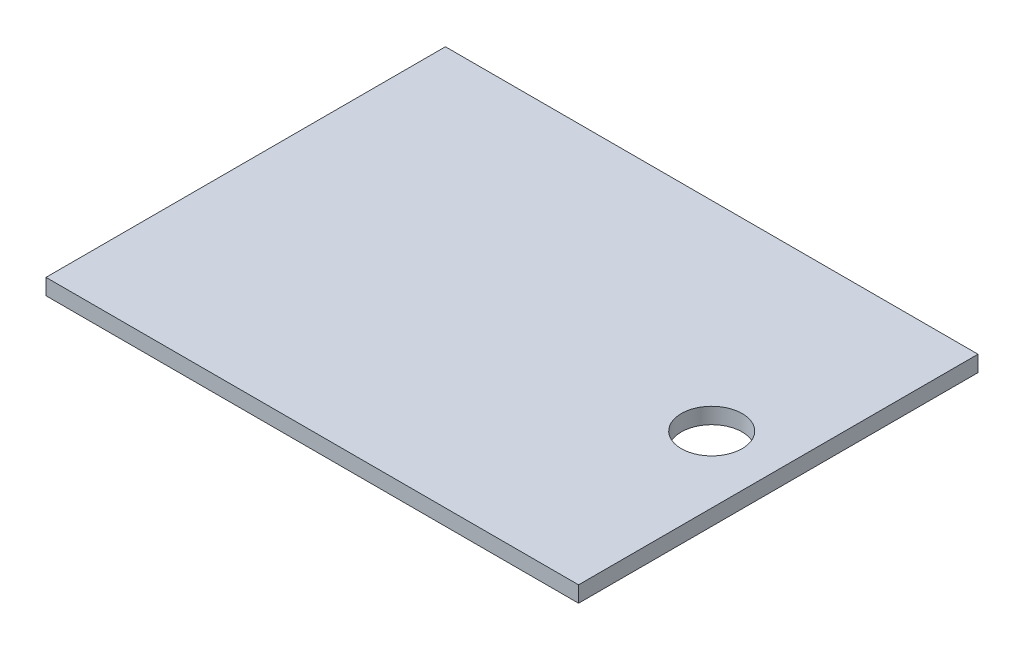
SolidWorks part; units mm, degrees
ref_plane "Front Plane" through (0, 0, 0) normal (0, 0, 1) x (1, 0, 0)
ref_plane "Top Plane" through (0, 0, 0) normal (0, 1, 0) x (1, 0, 0)
ref_plane "Right Plane" through (0, 0, 0) normal (1, 0, 0) x (0, 0, -1)
sketch "Sketch1" plane through (0, 0, 0) normal (0, 1, 0) x (1, 0, 0)
  line L1 (-100, 75) -> (100, 75)
  line L2 (-100, 75) -> (-100, -75)
  line L3 (-100, -75) -> (100, -75)
  line L4 (100, 75) -> (100, -75)
  circle A0 centre (75, 0) radius 11.43
  arc A1 (74.8502, -11.429) -> (75.1498, 11.429) centre (75, 0) ccw construction
  point P5 (0, -75)
  point P7 (100, 0)
  dimension "D1" = 200
  dimension "D2" = 150
  dimension "D3" = 75
extrude "Boss-Extrude1" add sketch "Sketch1" along normal blind 6
